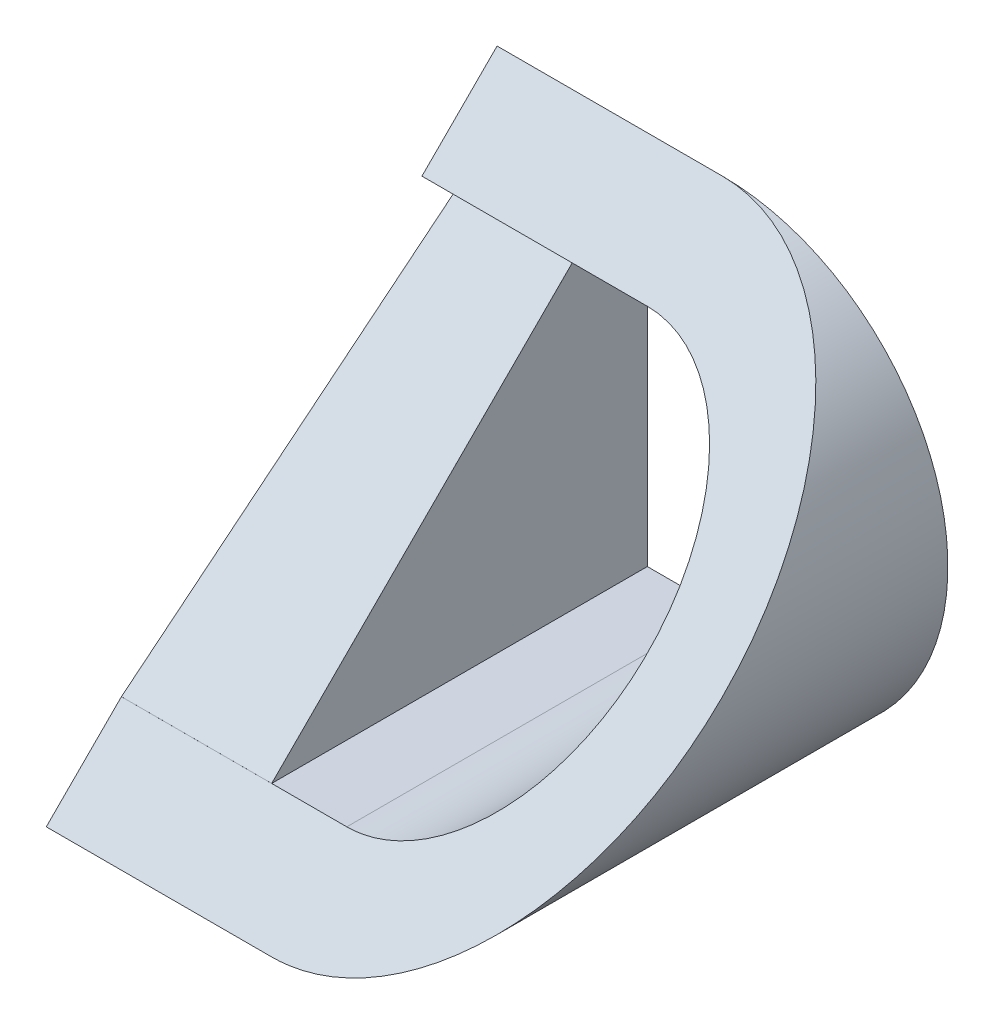
SolidWorks part; units mm, degrees
ref_plane "Front Plane" through (0, 0, 0) normal (0, 0, 1) x (1, 0, 0)
ref_plane "Top Plane" through (0, 0, 0) normal (0, 1, 0) x (1, 0, 0)
ref_plane "Right Plane" through (0, 0, 0) normal (1, 0, 0) x (0, 0, -1)
sketch "Sketch1" plane through (0, 0, 0) normal (0, 0, 1) x (1, 0, 0)
  line L1 (0, 0) -> (30, 0)
  line L2 (0, 0) -> (0, 60)
  line L3 (0, 60) -> (30, 60)
  line L4 (30, 0) -> (30, 60)
  arc A0 (30, 60) -> (30, 0) centre (30, 30) cw
  dimension "D1" = 30
  dimension "D2" = 60
extrude "Boss-Extrude1" add sketch "Sketch1" along normal blind 60 contours A0 L4 | L1 L4 L3 L2
sketch "Sketch2" plane through (0, 0, 0) normal (-1, 0, 0) x (0, 0, 1)
  line L0 (0, 60) -> (60, 0)
  line L1 (60, 0) -> (60, 60)
  line L2 (60, 60) -> (0, 60)
extrude "Cut-Extrude1" cut sketch "Sketch2" against normal blind 60
sketch "Sketch4" plane through (0, 0, 0) normal (0, 0, -1) x (-1, 0, 0)
  line L0 (0, 60) -> (0, 0) construction
  line L1 (-0.0001, 50) -> (-20.0001, 50)
  line L2 (-0.0001, 50) -> (-0.0001, 10)
  line L3 (-0.0001, 10) -> (-20.0001, 10)
  line L4 (-20.0001, 50) -> (-20.0001, 10)
  dimension "D1" = 20
  dimension "D2" = 0.0001
  dimension "D3" = 40
  dimension "D4" = 10
extrude "Cut-Extrude2" cut sketch "Sketch4" against normal blind 60
sketch "Sketch5" plane through (0, 0, 0) normal (0, 0, -1) x (-1, 0, 0)
  line L0 (-30, 50) -> (-20.0003, 50)
  line L1 (-20.0003, 50) -> (-20.0003, 10)
  line L2 (-20.0003, 10) -> (-30.0003, 10)
  line L3 (-20.0001, 50) -> (-20.0001, 10) construction
  arc A0 (-30, 50) -> (-30.0003, 10) centre (-30, 30) ccw
  dimension "D3" = 20
  dimension "D1" = 20
  dimension "D2" = 0.0002
  dimension "D4" = 10
  dimension "D5" = 9.9997
extrude "Cut-Extrude3" cut sketch "Sketch5" against normal blind 60
sketch "Sketch6" plane through (20.0001, 0, 0) normal (-1, 0, 0) x (0, 0, 1)
  line L0 (0, 50) -> (10, 50)
  line L1 (10, 50) -> (50, 10)
  line L2 (50, 10) -> (0, 10)
  line L3 (0, 10) -> (0, 50)
extrude "Boss-Extrude2" add sketch "Sketch6" along normal blind 20
sketch "Sketch7" plane through (0, 0, 0) normal (-1, 0, 0) x (0, 0, 1)
  line L0 (50, 10) -> (49.9969, 10)
  line L1 (50, 10) -> (0, 10) construction
  line L2 (49.9969, 10) -> (0.7483, 50)
  line L3 (0.7483, 50) -> (10, 50)
  line L4 (10, 50) -> (50, 10)
  point P7 (0, 0)
  point P10 (0.7483, 50)
  point P11 (49.9985, 10.0015)
extrude "Cut-Extrude9" cut sketch "Sketch7" against normal blind 20
